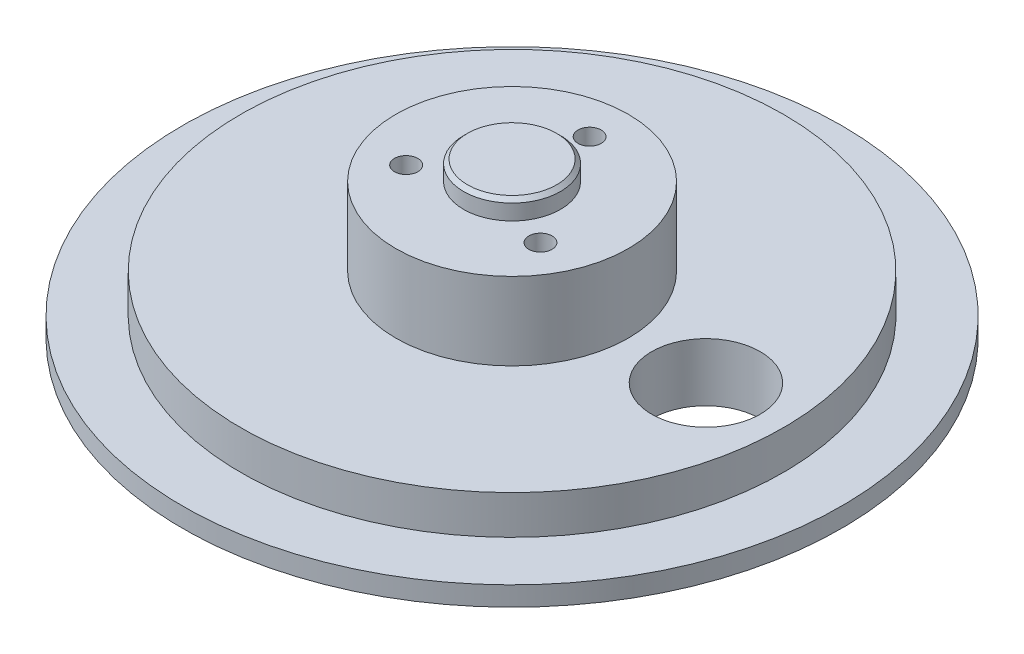
SolidWorks part; units mm, degrees
material "普通碳钢"
ref_plane "前视基准面" through (0, 0, 0) normal (0, 0, 1) x (1, 0, 0)
ref_plane "上视基准面" through (0, 0, 0) normal (0, 1, 0) x (1, 0, 0)
ref_plane "右视基准面" through (0, 0, 0) normal (1, 0, 0) x (0, 0, -1)
sketch "草图1" plane through (0, 0, 0) normal (0, 0, 1) x (1, 0, 0)
  line L0 (0, 0) -> (0, 15)
  line L1 (0, 0) -> (-85, 0)
  line L2 (-85, 0) -> (-85, 5)
  line L3 (-85, 5) -> (-70, 5)
  line L4 (-70, 5) -> (-70, 15)
  line L5 (-70, 15) -> (0, 15)
  dimension "D1" = 85
  dimension "D2" = 70
  dimension "D3" = 5
  dimension "D4" = 10
revolve "旋转1" add sketch "草图1" angle 360 about L0
sketch "草图2" plane through (0, 0, 0) normal (0, 1, 0) x (1, 0, 0)
  line L0 (0, 0) -> (70, 0) construction
  circle A0 centre (50, 0) radius 14
  circle A1 centre (0, 0) radius 50 construction
  circle A3 centre (0, 0) radius 70 construction
  point P18 (0, 0)
  dimension "D3" = 28
  dimension "D1" = 100
extrude "切除-拉伸1" cut sketch "草图2" along normal blind 20
sketch "草图3" plane through (0, 15, 0) normal (0, 1, 0) x (1, 0, 0)
  circle A0 centre (0, 0) radius 30
  dimension "D1" = 60
extrude "凸台-拉伸1" add sketch "草图3" along normal blind 20
sketch "草图4" plane through (0, 35, 0) normal (0, 1, 0) x (1, 0, 0)
  circle A0 centre (0, 0) radius 12.5
  dimension "D1" = 25
extrude "凸台-拉伸2" add sketch "草图4" along normal blind 5
chamfer "倒角1" distance 1 angle 45 1 edges at (0, 40, 12.5)
sketch "草图5" plane through (0, 35, 0) normal (0, 1, 0) x (1, 0, 0)
  circle A0 centre (0, 0) radius 20 construction
  circle A1 centre (0, 20) radius 3
  circle A2 centre (17.3205, -10) radius 3
  circle A3 centre (-17.3205, -10) radius 3
  point P12 (0, 0)
  dimension "D1" = 40
  dimension "D2" = 6
  dimension "D3" = 3
extrude "切除-拉伸2" cut sketch "草图5" against normal blind 15
